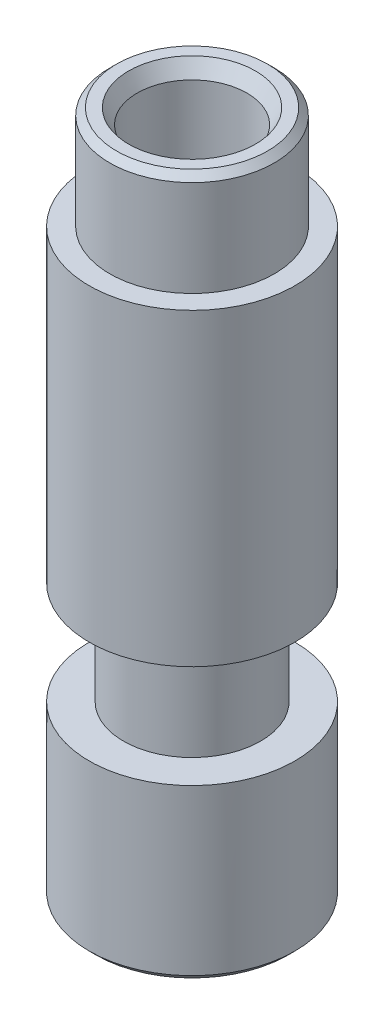
SolidWorks part; units mm, degrees
material "AISI 304"
ref_plane "Front Plane" through (0, 0, 0) normal (0, 0, 1) x (1, 0, 0)
ref_plane "Top Plane" through (0, 0, 0) normal (0, 1, 0) x (1, 0, 0)
ref_plane "Right Plane" through (0, 0, 0) normal (1, 0, 0) x (0, 0, -1)
sketch "Sketch1" plane through (0, 0, 0) normal (0, 1, 0) x (1, 0, 0)
  circle A0 centre (0, 0) radius 3
  dimension "D1" = 6
extrude "Boss-Extrude1" [suppressed] add sketch "Sketch1" along normal blind 7
cosmetic thread "Rosca cosmética1" [suppressed] parameters "D2"=5
sketch "Sketch2" [suppressed] plane through (0, 7, 0) normal (0, 1, 0) x (1, 0, 0)
  circle A0 centre (0, 0) radius 2.1
  dimension "D1" = 4.2
extrude "Boss-Extrude2" [suppressed] add sketch "Sketch2" along normal blind 2
sketch "Sketch3" [suppressed] plane through (0, 9, 0) normal (0, 1, 0) x (1, 0, 0)
  circle A0 centre (0, 0) radius 3
  dimension "D1" = 6
extrude "Boss-Extrude3" [suppressed] add sketch "Sketch3" along normal blind 6
cosmetic thread "Rosca cosmética2" parameters "D2"=5
sketch "Sketch4" [suppressed] plane through (0, 15, 0) normal (0, 1, 0) x (1, 0, 0)
  circle A0 centre (0, 0) radius 1.6
  dimension "D1" = 3.2
extrude "Cut-Extrude1" [suppressed] cut sketch "Sketch4" against normal through all
sketch "Croquis1" [suppressed] plane through (0, 15, 0) normal (0, 1, 0) x (1, 0, 0)
  circle A0 centre (0, 0) radius 2.4
  circle A1 centre (0, 0) radius 1.6
  circle A2 centre (0, 0) radius 1.6 construction
  dimension "D1" = 4.8
extrude "Saliente-Extruir1" [suppressed] add sketch "Croquis1" along normal blind 3
chamfer "Chaflán1" [suppressed] distance 0.2 angle 45
chamfer "Chaflán2" [suppressed] distance 0.2 angle 45
chamfer "Chaflán3" [suppressed] distance 0.25 angle 60
sketch "Croquis2" [suppressed] plane through (0, 0, 0) normal (0, 0, 1) x (1, 0, 0)
  line L0 (0, 17.8) -> (0, 0) construction
  line L1 (3, 11) -> (2.2, 11)
  line L2 (3, 11) -> (3, 5)
  line L3 (3, 5) -> (2.2, 5)
  line L4 (2.2, 11) -> (2.2, 5)
  line L5 (-3, 11) -> (-2.2, 11)
  line L6 (-3, 11) -> (-3, 5)
  line L7 (-3, 5) -> (-2.2, 5)
  line L8 (-2.2, 11) -> (-2.2, 5)
  line L9 (-2.4, 17.8) -> (2.4, 17.8) construction
  line L10 (-2.1, 8) -> (2.1, 8) construction
  line L11 (-2.1, 9) -> (-2.1, 7) construction
  line L12 (2.1, 7) -> (2.1, 9) construction
  line L13 (-3, 15) -> (-3, 9) construction
  line L14 (3, 9) -> (3, 15) construction
  dimension "D1" = 4.4
  dimension "D2" = 2.2
  dimension "D3" = 6
  dimension "D4" = 3
extrude "Cortar-Extruir1" [suppressed] cut sketch "Croquis2" against normal through all and the other way through all
sketch "Croquis3" plane through (0, 0, 0) normal (0, 0, 1) x (1, 0, 0)
  line L0 (-1.6, 0) -> (-1.6, 20)
  line L1 (-1.6, 20) -> (-2.4, 20)
  line L2 (-2.4, 20) -> (-2.4, 17)
  line L3 (-2.4, 17) -> (-3, 17)
  line L4 (-3, 17) -> (-3, 8)
  line L5 (-3, 8) -> (-2, 8)
  line L6 (-2, 8) -> (-2, 5)
  line L7 (-2, 5) -> (-3, 5)
  line L8 (-3, 5) -> (-3, 0)
  line L9 (-3, 0) -> (-1.6, 0)
  line L10 (0, 0) -> (0, 18.5179) construction
  dimension "D1" = 3.2
  dimension "D2" = 6
  dimension "D3" = 4.8
  dimension "D4" = 20
  dimension "D5" = 3
  dimension "D6" = 3
  dimension "D7" = 5
  dimension "D8" = 4
revolve "Revolución1" add sketch "Croquis3" angle 360 about L10
cosmetic thread "Rosca cosmética4" parameters "D2"=4.891
chamfer "Chaflán4" distance 0.2 angle 45 2 edges at (0, 20, -2.4) (0, 0, -3)
chamfer "Chaflán5" distance 0.25 angle 60 1 edges at (0, 20, -1.6)
sketch "Croquis4" [suppressed] plane through (0, 0, 0) normal (0, 0, 1) x (1, 0, 0)
  line L0 (2.1, 4) -> (2.1, 10) construction
  line L1 (2.1, 7) -> (2.25, 7)
  line L2 (2.1, 7) -> (2.1, 4)
  line L3 (2.1, 4) -> (2.25, 4)
  line L4 (2.25, 7) -> (2.25, 4)
  line L5 (0, 0) -> (0, 18.281) construction
  line L6 (3, 4) -> (-3, 4) construction
  dimension "D1" = 3
  dimension "D2" = 0.15
revolve "Revolución2" [suppressed] add sketch "Croquis4" angle 360 about L5
equation "\"D2@Croquis2\"=\"D1@Croquis2\"/2"
equation "\"D4@Croquis2\"=\"D3@Croquis2\"/2"
